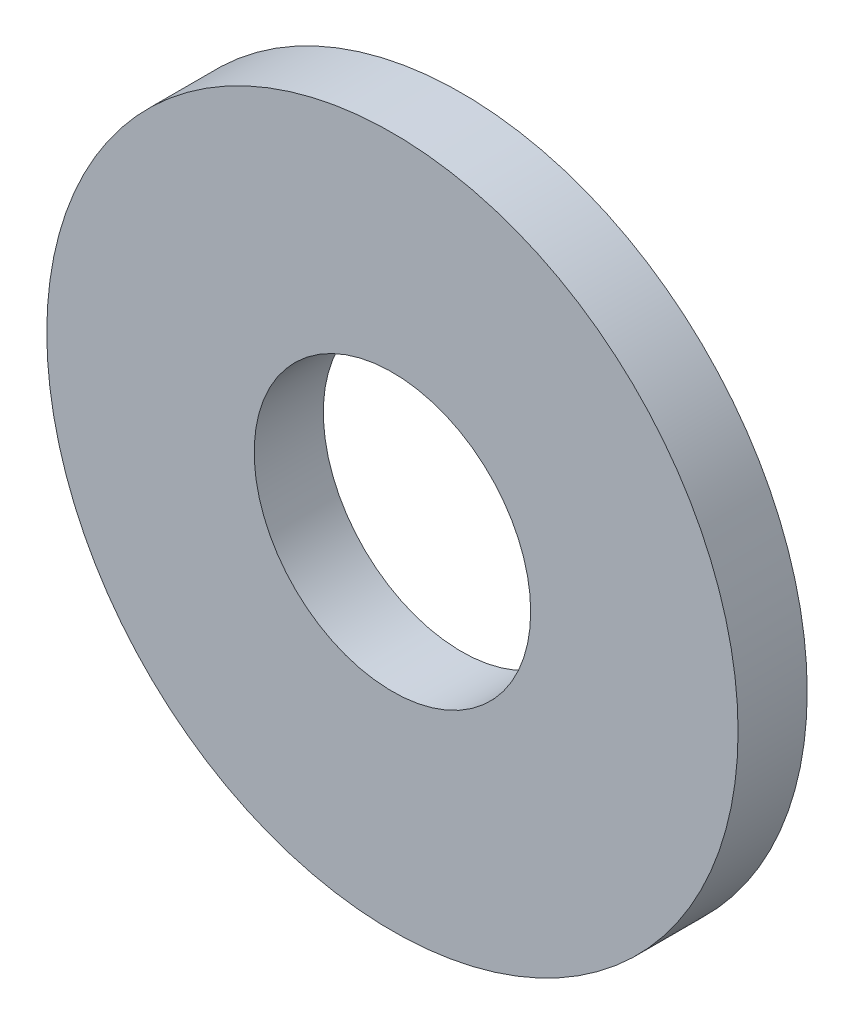
SolidWorks part; units mm, degrees
ref_plane "Front Plane" through (0, 0, 0) normal (0, 0, 1) x (1, 0, 0)
ref_plane "Top Plane" through (0, 0, 0) normal (0, 1, 0) x (1, 0, 0)
ref_plane "Right Plane" through (0, 0, 0) normal (1, 0, 0) x (0, 0, -1)
sketch "Sketch1" plane through (0, 0, 0) normal (0, 0, 1) x (1, 0, 0)
  circle A0 centre (0, 0) radius 5
  circle A1 centre (0, 0) radius 2
  dimension "D1" = 4
  dimension "D2" = 10
extrude "Boss-Extrude1" add sketch "Sketch1" along normal blind 1
